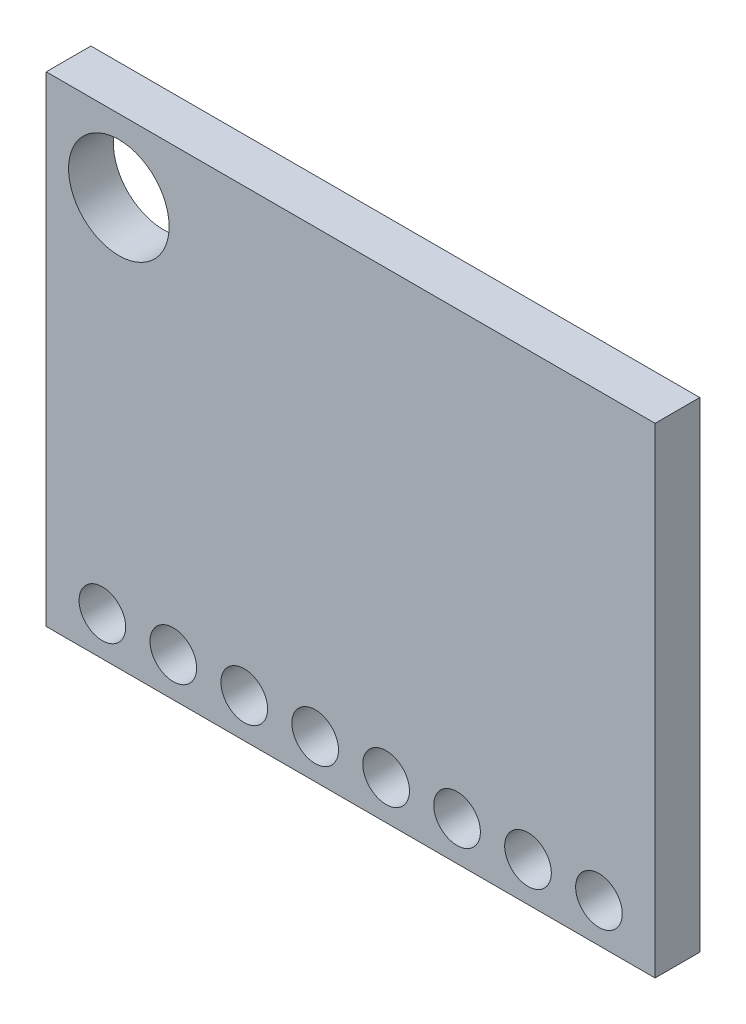
SolidWorks part; units mm, degrees
ref_plane "Front Plane" through (0, 0, 0) normal (0, 0, 1) x (1, 0, 0)
ref_plane "Top Plane" through (0, 0, 0) normal (0, 1, 0) x (1, 0, 0)
ref_plane "Right Plane" through (0, 0, 0) normal (1, 0, 0) x (0, 0, -1)
sketch "Sketch1" plane through (0, 0, 0) normal (0, 0, 1) x (1, 0, 0)
  line L1 (10.9, -8.6) -> (-10.9, -8.6)
  line L2 (10.9, -8.6) -> (10.9, 8.6)
  line L3 (10.9, 8.6) -> (-10.9, 8.6)
  line L4 (-10.9, -8.6) -> (-10.9, 8.6)
  line L5 (10.9, -8.6) -> (-10.9, 8.6) construction
  line L6 (10.9, 8.6) -> (-10.9, -8.6) construction
  point P0 (0, 0)
  dimension "D1" = 21.8
  dimension "D2" = 17.2
extrude "Boss-Extrude1" add sketch "Sketch1" along normal blind 1.6
sketch "Sketch2" plane through (0, 0, 1.6) normal (0, 0, 1) x (1, 0, 0)
  line L0 (10.9, -8.6) -> (10.9, 8.6) construction
  line L1 (-10.9, -8.6) -> (10.9, -8.6) construction
  line L2 (10.9, 8.6) -> (-10.9, 8.6) construction
  line L3 (-10.9, 8.6) -> (-10.9, -8.6) construction
  circle A0 centre (8.89, -7.2) radius 0.835
  circle A1 centre (6.35, -7.2) radius 0.835
  circle A2 centre (3.81, -7.2) radius 0.835
  circle A3 centre (1.27, -7.2) radius 0.835
  circle A4 centre (-1.27, -7.2) radius 0.835
  circle A5 centre (-3.81, -7.2) radius 0.835
  circle A6 centre (-6.35, -7.2) radius 0.835
  circle A7 centre (-8.89, -7.2) radius 0.835
  circle A8 centre (-8.3, 6) radius 1.8
  dimension "D3" = 1.67
  dimension "D5" = 2.6
  dimension "D6" = 2.6
  dimension "D7" = 3.6
  dimension "D1" = 2.01
  dimension "D2" = 1.4
  dimension "D4" = 8
extrude "Cut-Extrude1" cut sketch "Sketch2" against normal blind 1.6
